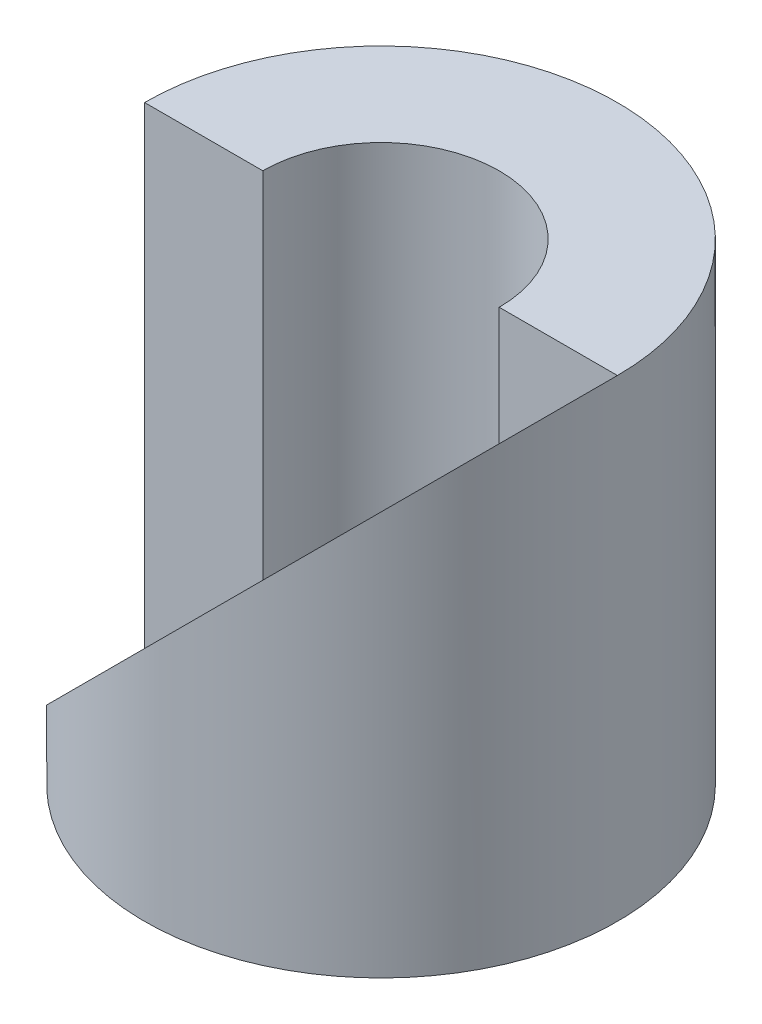
SolidWorks part; units mm, degrees
ref_plane "Front Plane" through (0, 0, 0) normal (0, 0, 1) x (1, 0, 0)
ref_plane "Top Plane" through (0, 0, 0) normal (0, 1, 0) x (1, 0, 0)
ref_plane "Right Plane" through (0, 0, 0) normal (1, 0, 0) x (0, 0, -1)
sketch "Sketch1" plane through (0, 0, 0) normal (0, 0, 1) x (1, 0, 0)
  line L1 (0, 0) -> (10, 0)
  line L2 (0, 0) -> (0, 20)
  line L3 (0, 20) -> (10, 20)
  line L4 (10, 0) -> (10, 20)
  dimension "D1" = 10
  dimension "D2" = 20
revolve "Revolve1" add sketch "Sketch1" angle 360 about L2
sketch "Sketch2" plane through (0, 20, 0) normal (0, 1, 0) x (1, 0, 0)
  circle A0 centre (0, 0) radius 5
  dimension "D1" = 10
extrude "Cut-Extrude4" cut sketch "Sketch2" against normal blind 20
sketch "Sketch4" plane through (0, 0, 0) normal (0, 0, 1) x (1, 0, 0)
  line L0 (10, 20) -> (-10, 0)
  line L1 (-10, 0) -> (-10, 20)
  line L2 (-10, 20) -> (10, 20)
extrude "Cut-Extrude5" cut sketch "Sketch4" along normal blind 10
